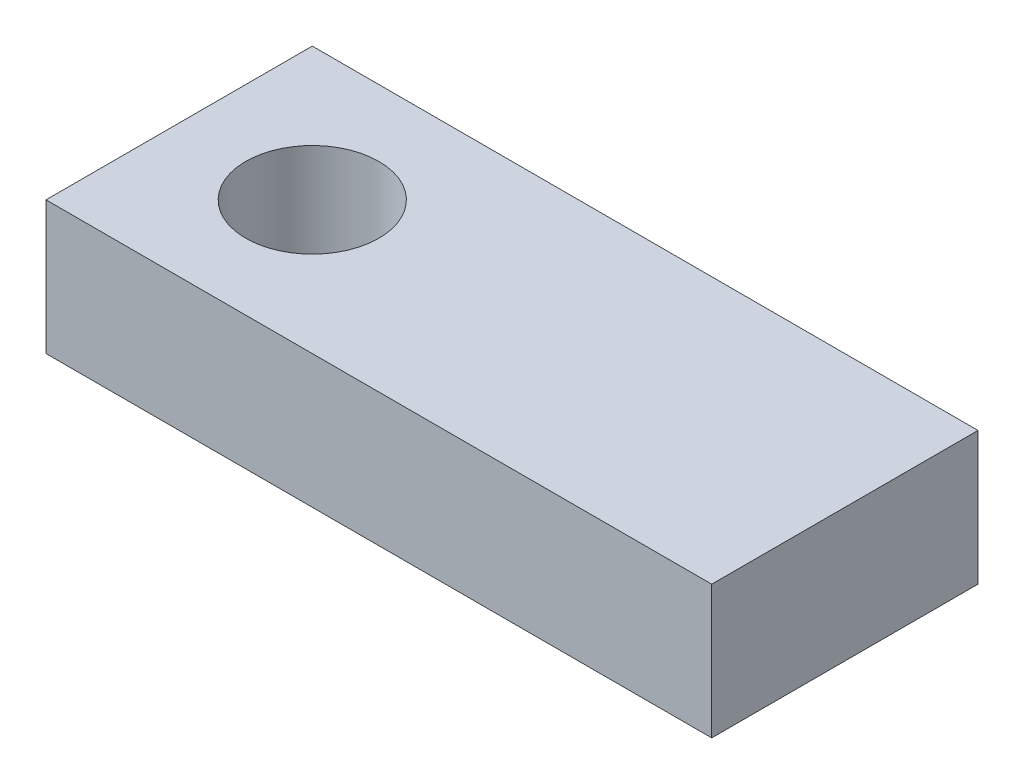
SolidWorks part; units mm, degrees
ref_plane "Front Plane" through (0, 0, 0) normal (0, 0, 1) x (1, 0, 0)
ref_plane "Top Plane" through (0, 0, 0) normal (0, 1, 0) x (1, 0, 0)
ref_plane "Right Plane" through (0, 0, 0) normal (1, 0, 0) x (0, 0, -1)
sketch "Sketch2" plane through (0, 0, 0) normal (0, 1, 0) x (1, 0, 0)
  line L1 (0, 0) -> (127, 0)
  line L2 (0, 0) -> (0, 50.8)
  line L3 (0, 50.8) -> (127, 50.8)
  line L4 (127, 0) -> (127, 50.8)
  dimension "D1" = 50.8
  dimension "D2" = 127
extrude "Boss-Extrude2" add sketch "Sketch2" along normal blind 25.4
sketch "Sketch3" plane through (0, 0, 0) normal (0, -1, 0) x (1, 0, 0)
  line L0 (0, -50.8) -> (0, 0) construction
  line L2 (0, -25.4) -> (25.4, -25.4) construction
  circle A0 centre (25.4, -25.4) radius 12.7
  dimension "D1" = 25.4
  dimension "D2" = 25.4
extrude "Cut-Extrude1" cut sketch "Sketch3" against normal up to next
